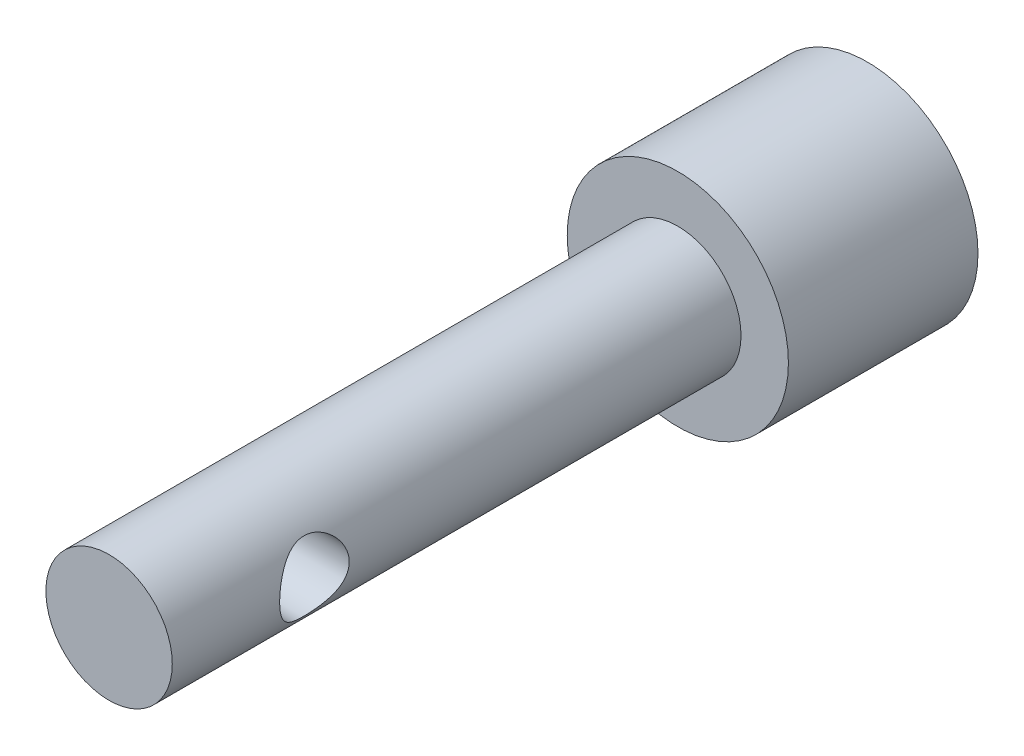
SolidWorks part; units mm, degrees
ref_plane "Płaszczyzna przednia" through (0, 0, 0) normal (0, 0, 1) x (1, 0, 0)
ref_plane "Płaszczyzna górna" through (0, 0, 0) normal (0, 1, 0) x (1, 0, 0)
ref_plane "Płaszczyzna prawa" through (0, 0, 0) normal (1, 0, 0) x (0, 0, -1)
sketch "Szkic1" plane through (0, 0, 0) normal (0, 0, 1) x (1, 0, 0)
  circle A0 centre (0, 0) radius 3.5
extrude "Dodanie-wyciągnięcie1" add sketch "Szkic1" along normal blind 6
sketch "Szkic2" plane through (0, 0, 6) normal (0, 0, 1) x (1, 0, 0)
  circle A0 centre (0, 0) radius 2
extrude "Dodanie-wyciągnięcie2" add sketch "Szkic2" along normal blind 18
ref_plane "Płaszczyzna1" through (-2, 0, 0) normal (-1, 0, 0) x (0, 0, 1)
sketch "Szkic3" plane through (-2, 0, 0) normal (-1, 0, 0) x (0, 0, 1)
  line L0 (6, -2) -> (6, 2) construction
  circle A0 centre (19.5, 0) radius 1.1
  dimension "12,5" = 13.5
extrude "Wytnij-wyciągnięcie1" cut sketch "Szkic3" against normal through all
sketch "Szkic4" plane through (0, 0, 0) normal (0, 0, -1) x (-1, 0, 0)
  circle A0 centre (0, 0) radius 2.3
  dimension "D1" = 4.6
extrude "Wytnij-wyciągnięcie2" cut sketch "Szkic4" against normal blind 3
